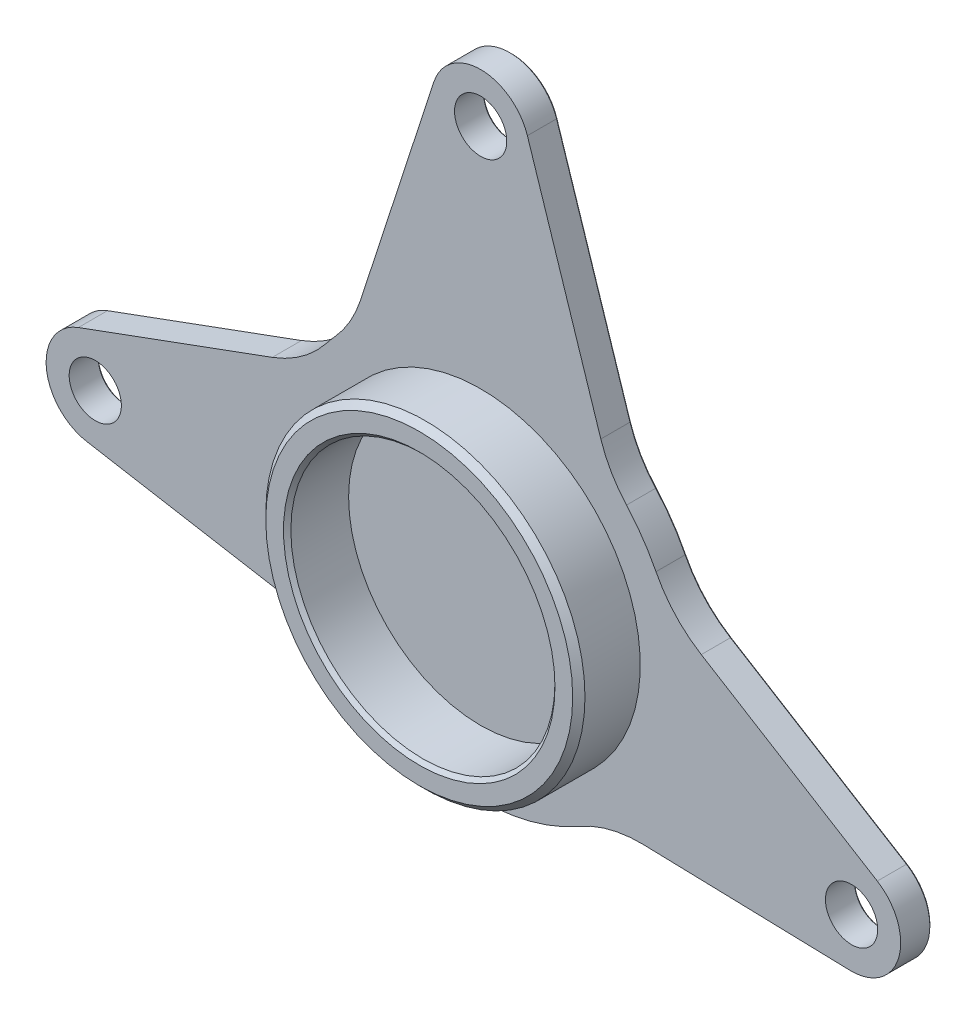
SolidWorks part; units mm, degrees
material "7075-T6 (SN)"
ref_plane "Plan de face" through (0, 0, 0) normal (0, 0, 1) x (1, 0, 0)
ref_plane "Plan de dessus" through (0, 0, 0) normal (0, 1, 0) x (1, 0, 0)
ref_plane "Plan de droite" through (0, 0, 0) normal (1, 0, 0) x (0, 0, -1)
sketch "Esquisse1" plane through (0, 0, 0) normal (0, 0, 1) x (1, 0, 0)
  circle A0 centre (0, 0) radius 25.985
  circle A1 centre (0, 0) radius 21.5
  dimension "D1" = 51.97
  dimension "D2" = 43
extrude "Boss.-Extru.1" add sketch "Esquisse1" along normal blind 10
chamfer "Chanfrein1" distance 1 angle 45 1 edges at (25.985, 0, 10)
chamfer "Chanfrein2" distance 0.6 angle 45 1 edges at (21.5, 0, 10)
sketch "Esquisse2" plane through (0, 0, 0) normal (0, 0, -1) x (-1, 0, 0)
  line L0 (7.6085, 65.4721) -> (19.5628, 28.6806)
  line L1 (0, 63) -> (0, 0) construction
  line L2 (0, 0) -> (-60.3857, -17.9603) construction
  line L3 (0, 0) -> (62.7468, -5.6429) construction
  line L4 (-7.6085, 65.4721) -> (-19.5628, 28.6806)
  line L5 (65.5011, 1.868) -> (33.9256, 13.4473)
  line L6 (64.1169, -13.5247) -> (30.982, -19.2845)
  line L7 (-26.5481, -25.0395) -> (-60.1673, -25.9573)
  line L8 (-35.9171, 6.4607) -> (-64.5732, -11.1439)
  arc A0 (-23.7439, 21.4529) -> (-28.5453, 14.4626) centre (0, 0) ccw
  circle A1 centre (0, 63) radius 4.25
  circle A2 centre (62.7468, -5.6429) radius 4.25
  circle A3 centre (-60.3857, -17.9603) radius 4.25
  circle A4 centre (0, 0) radius 63 construction
  arc A5 (64.1169, -13.5247) -> (65.5011, 1.868) centre (62.7468, -5.6429) ccw
  arc A6 (7.6085, 65.4721) -> (-7.6085, 65.4721) centre (0, 63) ccw
  arc A7 (-64.5732, -11.1439) -> (-60.1673, -25.9573) centre (-60.3857, -17.9603) ccw
  arc A8 (-16.0014, -27.712) -> (21.1737, -23.9932) centre (0, 0) ccw
  arc A9 (25.1148, 19.8305) -> (23.7439, 21.4529) centre (0, 0) ccw
  arc A10 (30.982, -19.2845) -> (21.1737, -23.9932) centre (34.4072, -38.989) ccw
  arc A11 (-26.5481, -25.0395) -> (-16.0014, -27.712) centre (-26.0023, -45.032) cw
  arc A12 (-35.9171, 6.4607) -> (-28.5453, 14.4626) centre (-46.3861, 23.5018) ccw
  arc A13 (-19.5628, 28.6806) -> (-23.7439, 21.4529) centre (-38.5839, 34.8609) cw
  arc A14 (33.9256, 13.4473) -> (25.1148, 19.8305) centre (40.8115, 32.2245) cw
  arc A15 (19.5628, 28.6806) -> (23.7439, 21.4529) centre (38.5839, 34.8609) ccw
  point P12 (24.6695, -20.3818)
  point P26 (-20.1433, -24.8646)
  point P33 (27.9101, 15.6533)
  dimension "D1" = 64
  dimension "D4" = 126
  dimension "D6" = 8.5
  dimension "D7" = 8.5
  dimension "D8" = 8.5
  dimension "D9" = 16
  dimension "D10" = 16
  dimension "D11" = 16
  dimension "D18" = 20
  dimension "D2" = 93
  dimension "D3" = 101
  dimension "D5" = 123.747
  dimension "D12" = 18
  dimension "D13" = 18
  dimension "D14" = 15
  dimension "D15" = 15
  dimension "D16" = 15
  dimension "D17" = 15
extrude "Boss.-Extru.2" add sketch "Esquisse2" along normal blind 5
chamfer "Chanfrein3" distance 0.25 angle 45 21 edges at (56.1357, -17.9603, -5) (-4.25, 63, -5) (-70.7146, -6.3594, -5) (-47.5494, -16.4046, -5) (-25.7515, -20.9591, -5) (-3.1852, -31.8411, -5) (21.0895, -25.6448, -5) (43.3577, -25.4984, -5) (68.0537, -20.241, -5) (50.2452, -2.3416, -5) (31.6766, 9.9507, -5) (26.3772, 18.1175, -5) (21.2719, 24.8461, -5) (13.5856, 47.0764, -5) (0, 71, -5) (-13.5856, 47.0764, -5) (-21.2719, 24.8461, -5) (-24.4428, 20.6531, -5) (-29.0778, 16.0282, -5) (-49.7134, 7.6577, -5) (-66.9968, -5.6429, -5)
